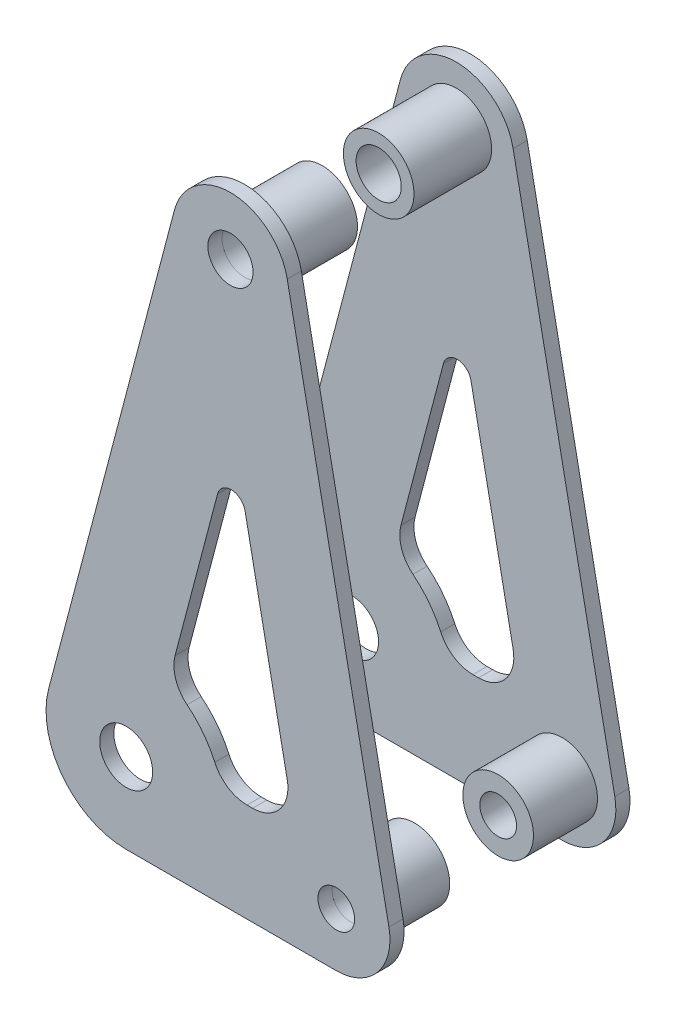
SolidWorks part; units mm, degrees
material "AISI 4130 Steel, normalized at 870C"
ref_plane "Front Plane" through (0, 0, 0) normal (0, 0, 1) x (1, 0, 0)
ref_plane "Top Plane" through (0, 0, 0) normal (0, 1, 0) x (1, 0, 0)
ref_plane "Right Plane" through (0, 0, 0) normal (1, 0, 0) x (0, 0, -1)
sketch "Sketch4" plane through (0, 0, 0) normal (0, 0, 1) x (1, 0, 0)
  line L0 (-13.9388, 3.6724) -> (8.6872, 89.5517)
  line L1 (0, -14.4145) -> (37.8012, -14.4145)
  line L2 (18.7576, 86.8986) -> (0, 0) construction
  line L3 (0, 0) -> (37.8012, -4.7625) construction
  line L4 (55, 0) -> (-55, 0) construction
  line L5 (28.9708, 88.9339) -> (47.267, -2.8761)
  line L6 (16.4368, 49.1773) -> (8.7932, 20.1656)
  line L7 (21.7404, 3.3655) -> (22.7432, 3.3655)
  line L8 (28.9707, 10.9566) -> (21.384, 49.0266)
  arc A0 (0, -14.4145) -> (-13.9388, 3.6724) centre (0, 0) cw
  circle A1 centre (18.7576, 86.8986) radius 4.064
  circle A2 centre (37.8012, -4.7625) radius 3.302
  arc A3 (8.6872, 89.5517) -> (28.9708, 88.9339) centre (18.7576, 86.8986) cw
  arc A4 (37.8012, -14.4145) -> (47.267, -2.8761) centre (37.8012, -4.7625) ccw
  arc A5 (16.4368, 49.1773) -> (21.384, 49.0266) centre (18.893, 48.5302) cw
  circle A6 centre (0, 0) radius 4.7625
  arc A7 (28.9707, 10.9566) -> (22.7432, 3.3655) centre (22.7432, 9.7155) cw
  arc A8 (8.7932, 20.1656) -> (10.9514, 13.6017) centre (14.9337, 18.5478) ccw
  arc A9 (10.9514, 13.6017) -> (15.9429, 7.1247) centre (0, 0) cw
  arc A10 (15.9429, 7.1247) -> (21.7404, 3.3655) centre (21.7404, 9.7155) ccw
  dimension "D4" = 6.35
  dimension "D5" = 9.652
  dimension "D6" = 6.35
  dimension "D7" = 8.128
  dimension "D8" = 6.604
  dimension "D9" = 9.525
  dimension "D10" = 15.24
  dimension "D11" = 17.78
  dimension "D12" = 12.7
  dimension "D13" = 2.54
  dimension "D14" = 17.78
  dimension "D16" = 6.35
  dimension "D1" = 38.1
  dimension "D2" = 88.9
  dimension "D3" = 85
  dimension "D15" = 17.78
extrude "Bellcrank Plate" add sketch "Sketch4" along normal blind 2.54 from offset 19.05 separate body
sketch "Sketch5" plane through (0, 0, 19.05) normal (0, 0, -1) x (-1, 0, 0)
  circle A1 centre (-37.8012, -4.7625) radius 3.302 construction
  circle A3 centre (-37.8012, -4.7625) radius 3.302
  circle A5 centre (-37.8012, -4.7625) radius 6.35
  dimension "D1" = 12.7
extrude "Pull Rod Washer" add sketch "Sketch5" along normal blind 11.5189 separate body
sketch "Sketch6" plane through (0, 0, 19.05) normal (0, 0, -1) x (-1, 0, 0)
  circle A0 centre (-18.7576, 86.8986) radius 6.35
  circle A3 centre (-37.8012, -4.7625) radius 6.35 construction
  circle A4 centre (-18.7576, 86.8986) radius 4.064 construction
  circle A5 centre (-18.7576, 86.8986) radius 4.064
extrude "Damper Washer" add sketch "Sketch6" along normal blind 13.97 separate body
mirror "Bellcrank Mirror" about plane through (0, 0, 0) normal (0, 0, 1) of bodies 103 105 109 106
